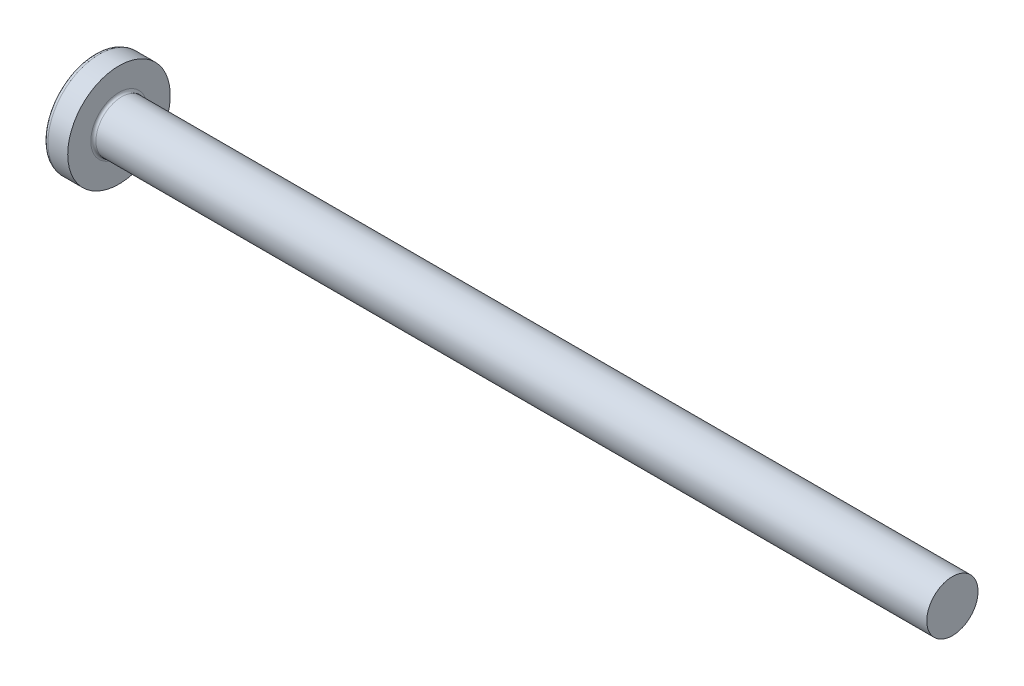
SolidWorks part; units mm, degrees
ref_plane "Plane1" through (0, 0, 0) normal (0, 0, 1) x (1, 0, 0)
ref_plane "Plane2" through (0, 0, 0) normal (0, 1, 0) x (1, 0, 0)
ref_plane "Plane3" through (0, 0, 0) normal (1, 0, 0) x (0, 0, -1)
sketch "BodySke" plane through (0, 0, 0) normal (0, 0, 1) x (1, 0, 0)
  line L0 (3.1, 2) -> (3.1, 4)
  line L1 (3.45, 6.35) -> (3.45, -3.175) construction
  line L2 (-25.4, 0) -> (127, 0) construction
  line L3 (68.1, 0) -> (0, 0)
  line L4 (3.1, 2) -> (68.1, 2)
  line L5 (68.1, 2) -> (68.1, 0)
  line L6 (1.5553, 4) -> (3.1, 4)
  line L8 (3.1, 6.35) -> (3.1, -3.175) construction
  arc A0 (1.2654, 3.8534) -> (0, 0) centre (6.5, 0) ccw
  arc A2 (1.2654, 3.8534) -> (1.5553, 4) centre (1.5553, 3.64) cw
  dimension "Head_crown_rad" = 6.5
  dimension "Head_fillet_rad" = 0.36
  dimension "Length" = 65
  dimension "Head_ht" = 3.1
  dimension "Head_dia" = 8
  dimension "Advance" = 0.7
  dimension "Thread_nom" = 65
  dimension "Diameter" = 4
revolve "Base-Revolve" add sketch "BodySke"
cosmetic thread "ThreadCosmetic" [suppressed]
fillet "Fillet1" radius 0.2 1 edges at (3.1, 0, 2)
sketch "Sketch3" plane through (0, 0, 0) normal (1, 0, 0) x (0, 0, -1)
  line L0 (0.515, -2.15) -> (-0.515, -2.15)
  line L1 (0.515, -2.15) -> (0.515, 2.15)
  line L2 (-0.515, 2.15) -> (0.515, 2.15)
  line L3 (-0.515, 2.15) -> (-0.515, -2.15)
  dimension "Cross_dia" = 4.3
  dimension "D1" = 2.15
  dimension "Cross_width" = 1.03
  dimension "D2" = 0.515
ref_plane "Plane4" through (2.34, 0, 0) normal (1, 0, 0) x (0, 0, -1)
sketch "Sketch4" plane through (2.34, 0, 0) normal (1, 0, 0) x (0, 0, -1)
  line L0 (0.515, -0.9833) -> (-0.515, -0.9833)
  line L1 (0.515, -0.9833) -> (0.515, 0.9833)
  line L2 (-0.515, 0.9833) -> (0.515, 0.9833)
  line L3 (-0.515, 0.9833) -> (-0.515, -0.9833)
  dimension "D1" = 1.03
  dimension "D2" = 1.9666
  dimension "D3" = 0.515
  dimension "D4" = 0.9833
loft "Recess" cut profiles "Sketch3", "Sketch4"
pattern_circular "RecPat" count 2 every 90 about axis through (0, 0, 0) along (1, 0, 0) of "Recess"
sketch "RecCorSke" plane through (0, 0, 0) normal (0, 0, 1) x (1, 0, 0)
  line L0 (-3.175, 0) -> (15.875, 0) construction
  line L1 (-25.4, 0) -> (127, 0) construction
  line L2 (0, 0) -> (0, 1.0146)
  line L3 (0, 1.0146) -> (2.34, 0.851)
  line L4 (2.34, 0.851) -> (2.6165, 0)
  line L5 (2.6165, 0) -> (0, 0)
  dimension "Diameter" = 1.702
  dimension "Depth" = 2.34
  dimension "Draft_angle" = 4
  dimension "Bottom_angle" = 18
revolve "RecessCore" cut sketch "RecCorSke" angle 360 about L0
sketch "ThdSchSke" plane through (0, 0, 0) normal (0, 0, 1) x (1, 0, 0)
  line L0 (4.5, -1.61) -> (4.2269, -2)
  line L1 (4.5, -1.61) -> (4.7731, -2)
  line L2 (4.7731, -2) -> (4.7731, -2.5)
  line L3 (-3.175, 0) -> (5.1513, 0) construction
  line L5 (4.7731, -2.5) -> (4.2269, -2.5)
  line L6 (4.2269, -2.5) -> (4.2269, -2)
  dimension "Diameter" = 4
  dimension "SideAngle" = 55
  dimension "VeeAngle" = 70
  dimension "Thread_minor" = 3.22
  dimension "Overcut" = 5
  dimension "Start" = 4.5
revolve "ThreadSchematic" [suppressed] cut sketch "ThdSchSke" angle 360 about L3
pattern_linear "ThdSchPat" [suppressed]
equation "\"D1@Sketch3\" = \"Cross_dia@Sketch3\" / 2"
equation "\"D2@Sketch3\" = \"Cross_width@Sketch3\" / 2"
equation "\"Depth@RecCorSke\" = \"Cross_depth@Plane4\""
equation "\"D1@Sketch4\" = \"Cross_width@Sketch3\""
equation "\"D2@Sketch4\" = \"Cross_dia@Sketch3\" - 2.0 * \"Cross_depth@Plane4\" * tan(26.5  * 0.017453292)"
equation "\"D3@Sketch4\" = \"D1@Sketch4\" / 2"
equation "\"D4@Sketch4\" = \"D2@Sketch4\" / 2"
equation "\"Thread_length@ThreadCosmetic\" = ((sgn( (\"Length@BodySke\" - \"Advance@BodySke\" * 2.0 ) - \"Thread_nom@BodySke\" )-1)*( (\"Length@BodySke\" - \"Advance@BodySke\" * 2.0 ) - \"Thread_nom@BodySke\" ))/-2+ \"Thread_nom@BodySke\""
equation "\"Thread_minor@ThdSchSke\" = \"Thread_minor@ThreadCosmetic\""
equation "\"Diameter@ThdSchSke\" = \"Diameter@BodySke\""
equation "\"Overcut@ThdSchSke\" = \"Diameter@BodySke\" * 1.25"
equation "\"Start@ThdSchSke\" = \"Head_ht@BodySke\" + \"Length@BodySke\" - \"Thread_length@ThreadCosmetic\"  '---Non-countersunk---"
equation "\"Num_threads@ThdSchPat\" = int( \"Thread_length@ThreadCosmetic\" / \"Advance@BodySke\" + 0.999 )  + 1"
equation "\"Advance@ThdSchPat\" = \"Thread_length@ThreadCosmetic\" /  (\"Num_threads@ThdSchPat\" - 1) 'relax it"
